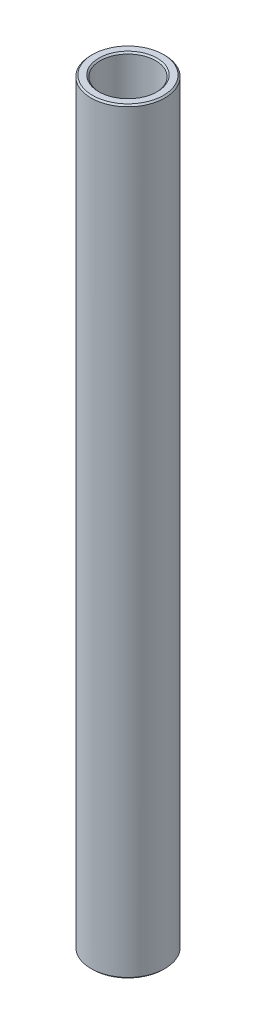
SolidWorks part; units mm, degrees
ref_plane "Front Plane" through (0, 0, 0) normal (0, 0, 1) x (1, 0, 0)
ref_plane "Top Plane" through (0, 0, 0) normal (0, 1, 0) x (1, 0, 0)
ref_plane "Right Plane" through (0, 0, 0) normal (1, 0, 0) x (0, 0, -1)
sketch "Sketch1" plane through (0, 0, 0) normal (0, 0, 1) x (1, 0, 0)
  line L0 (0, 11.6086) -> (0, -11.6086) construction
  line L1 (4.7625, 65.0875) -> (6.35, 65.0875)
  line L2 (6.35, 65.0875) -> (6.35, -65.0875)
  line L3 (6.35, -65.0875) -> (4.7625, -65.0875)
  line L4 (4.7625, -65.0875) -> (4.7625, 65.0875)
  line L5 (4.7625, 0) -> (0, 0) construction
  dimension "D1" = 9.525
  dimension "D2" = 12.7
  dimension "D3" = 130.175
revolve "Revolve1" add sketch "Sketch1" angle 360 about L0
chamfer "Chamfer1" distance 0.254 angle 45 4 edges at (-4.7625, -65.0875, 0) (-6.35, -65.0875, 0) (-6.35, 65.0875, 0) (-4.7625, 65.0875, 0)
